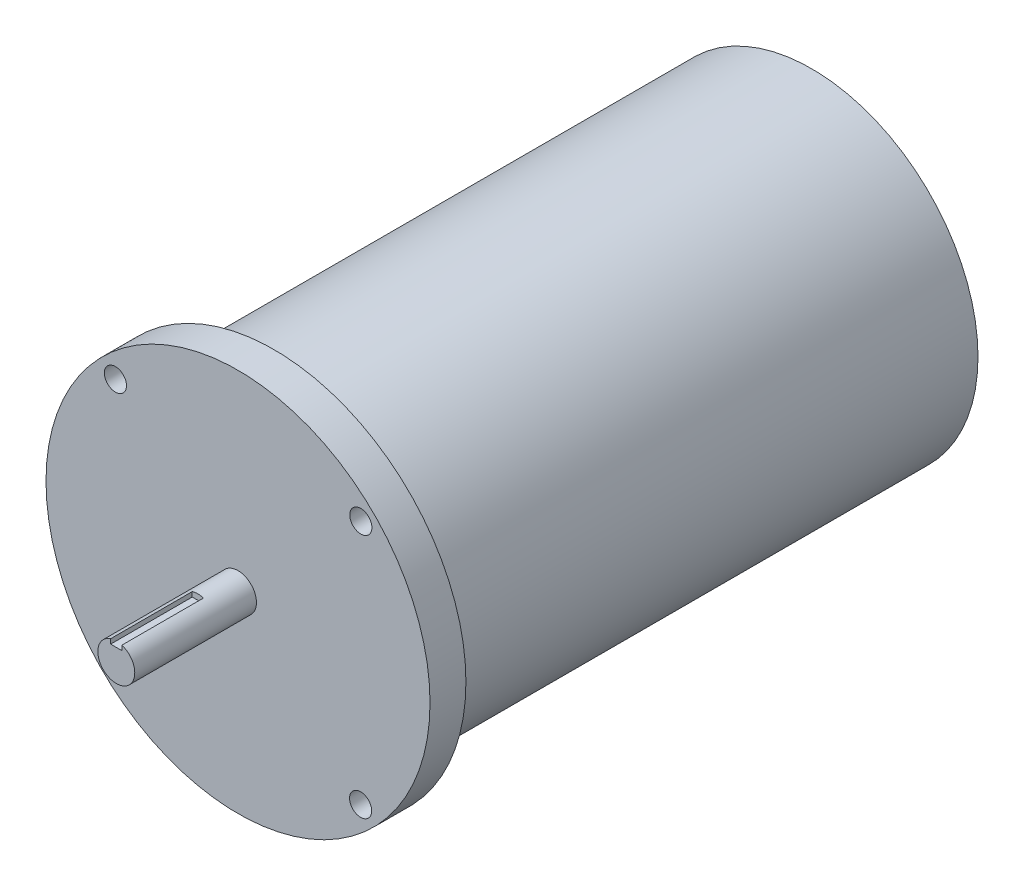
SolidWorks part; units mm, degrees
ref_plane "Front Plane" through (0, 0, 0) normal (0, 0, 1) x (1, 0, 0)
ref_plane "Top Plane" through (0, 0, 0) normal (0, 1, 0) x (1, 0, 0)
ref_plane "Right Plane" through (0, 0, 0) normal (1, 0, 0) x (0, 0, -1)
sketch "Sketch2" plane through (0, 0, 0) normal (0, 0, 1) x (1, 0, 0)
  circle A0 centre (0, 0) radius 71.501
  dimension "D1" = 143.002
extrude "Boss-Extrude1" add sketch "Sketch2" along normal blind 231.2
sketch "Sketch3" plane through (0, 0, 231.2) normal (0, 0, 1) x (1, 0, 0)
  circle A0 centre (0, 0) radius 82.55
  circle A1 centre (-52.7141, 52.8039) radius 4.7625
  circle A2 centre (52.8039, 52.7141) radius 4.7625
  circle A3 centre (52.7141, -52.8039) radius 4.7625
  circle A4 centre (-52.8039, -52.7141) radius 4.7625
  point P13 (0, 0)
  dimension "D1" = 165.1
  dimension "D2" = 9.525
  dimension "D3" = 74.6125
  dimension "D4" = 52.8039
  dimension "D5" = 4
extrude "Boss-Extrude2" add sketch "Sketch3" along normal blind 15.434
sketch "Sketch4" plane through (0, 0, 246.634) normal (0, 0, 1) x (1, 0, 0)
  circle A0 centre (0, 0) radius 7.9375
  dimension "D1" = 15.875
extrude "Boss-Extrude3" add sketch "Sketch4" along normal blind 52.324
sketch "Sketch5" plane through (0, 0, 298.958) normal (0, 0, 1) x (1, 0, 0)
  line L1 (-2.413, 10.3505) -> (2.413, 10.3505)
  line L2 (-2.413, 10.3505) -> (-2.413, 5.5245)
  line L3 (-2.413, 5.5245) -> (2.413, 5.5245)
  line L4 (2.413, 10.3505) -> (2.413, 5.5245)
  line L5 (-2.413, 10.3505) -> (2.413, 5.5245) construction
  line L6 (-2.413, 5.5245) -> (2.413, 10.3505) construction
  circle A0 centre (0, 0) radius 7.9375 construction
  circle A1 centre (0, 0) radius 7.9375 construction
  point P0 (0, 7.9375)
  dimension "D1" = 4.826
  dimension "D2" = 4.826
extrude "Cut-Extrude1" cut sketch "Sketch5" against normal blind 35.052
